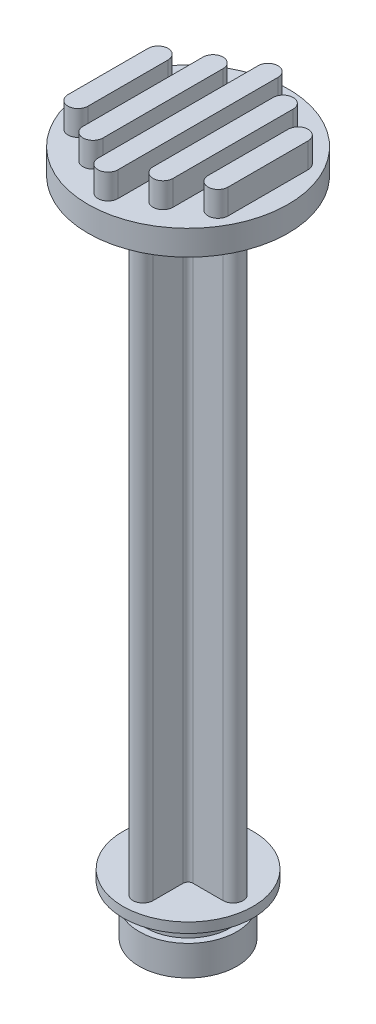
SolidWorks part; units mm, degrees
ref_plane "Front Plane" through (0, 0, 0) normal (0, 0, 1) x (1, 0, 0)
ref_plane "Top Plane" through (0, 0, 0) normal (0, 1, 0) x (1, 0, 0)
ref_plane "Right Plane" through (0, 0, 0) normal (1, 0, 0) x (0, 0, -1)
sketch "Sketch1" plane through (0, 0, 0) normal (0, 0, 1) x (1, 0, 0)
  line L0 (0, 0) -> (4.875, 0)
  line L1 (4.875, 0) -> (4.875, 3)
  line L2 (4.875, 3) -> (4.225, 3)
  line L3 (4.225, 3) -> (4.225, 5)
  line L4 (4.225, 5) -> (6.5, 5)
  line L5 (6.5, 5) -> (6.5, 6)
  line L6 (6.5, 6) -> (0, 6)
  line L7 (0, 6) -> (0, 0)
  dimension "D1" = 6.5
  dimension "D2" = 1
  dimension "D3" = 2
  dimension "D4" = 3
  dimension "D5" = 4.875
  dimension "D6" = 4.225
revolve "Revolve1" add sketch "Sketch1" angle 360 about L7
sketch "Sketch2" plane through (0, 6, 0) normal (0, 1, 0) x (1, 0, 0)
  line L0 (0, 1) -> (0, 0) construction
  line L1 (-1, 0) -> (0, 0) construction
  line L2 (-1, 4.5) -> (-1, 1.5)
  line L3 (-4.5, -1) -> (-1.5, -1)
  line L4 (1, 4.5) -> (1, 1.5)
  line L5 (-4.5, 1) -> (-1.5, 1)
  line L6 (-1, 6.5) -> (-1, -6.5) construction
  line L7 (0, 6.5) -> (0, -6.5) construction
  line L8 (1, 6.5) -> (1, -6.5) construction
  line L9 (-6.5, 1) -> (6.5, 1) construction
  line L10 (-6.5, 0) -> (6.5, 0) construction
  line L11 (-6.5, -1) -> (6.5, -1) construction
  line L12 (1.5, -1) -> (4.5, -1)
  line L13 (0, -1) -> (0, -5.5) construction
  line L14 (1, -1.5) -> (1, -4.5)
  line L15 (1.5, 1) -> (4.5, 1)
  line L16 (-1, -1.5) -> (-1, -4.5)
  arc A1 (1, 4.5) -> (-1, 4.5) centre (0, 4.5) ccw
  arc A2 (4.5, -1) -> (4.5, 1) centre (4.5, 0) ccw
  arc A3 (1, -4.5) -> (-1, -4.5) centre (0, -4.5) cw
  arc A4 (-4.5, -1) -> (-4.5, 1) centre (-4.5, 0) cw
  arc A5 (-1.5, 1) -> (-1, 1.5) centre (-1.5, 1.5) ccw
  arc A6 (1, 1.5) -> (1.5, 1) centre (1.5, 1.5) ccw
  arc A7 (1.5, -1) -> (1, -1.5) centre (1.5, -1.5) ccw
  arc A8 (-1, -1.5) -> (-1.5, -1) centre (-1.5, -1.5) ccw
  point P42 (1, -1)
  point P45 (-1, -1)
  dimension "D5" = 0.5
  dimension "D3" = 4.5
  dimension "D4" = 4.5
  dimension "D1" = 1
  dimension "D2" = 1
extrude "Boss-Extrude1" add sketch "Sketch2" along normal blind 60
sketch "Sketch3" plane through (0, 66, 0) normal (0, 1, 0) x (1, 0, 0)
  circle A0 centre (0, 0) radius 10
  dimension "D1" = 20
extrude "Boss-Extrude2" add sketch "Sketch3" along normal blind 2.5
sketch "Sketch4" plane through (0, 68.5, 0) normal (0, 1, 0) x (1, 0, 0)
  line L0 (0, 6.3392) -> (0, -10) construction
  line L1 (-10, 0) -> (10, 0) construction
  line L2 (-3.5, 4.0448) -> (-3.5, -6.1505) construction
  line L3 (-1, 10) -> (-1, -10) construction
  line L4 (-1, 8) -> (-1, -10)
  line L5 (-4.5, 6) -> (-4.5, -6.1505)
  line L6 (-8, 4) -> (-8, -4)
  line L7 (1, 8) -> (1, -10)
  line L8 (-2.5, 6) -> (-2.5, -6.1505)
  line L9 (-6, -4) -> (-6, 4)
  line L10 (-4.5, 6.5652) -> (-4.5, -6.1505) construction
  line L11 (-3.5, 6.5652) -> (-3.5, -6.1505) construction
  line L12 (-2.5, 6.5652) -> (-2.5, -6.1505) construction
  line L13 (0, 10) -> (0, -10) construction
  line L14 (1, 10) -> (1, -10) construction
  line L15 (7, 0) -> (7, -3.9115) construction
  line L16 (-7, 0) -> (-7, -3.9115) construction
  line L17 (3.5, 4.0448) -> (3.5, -6.1505) construction
  line L18 (6, -4) -> (6, 4)
  line L19 (2.5, 6) -> (2.5, -6.1505)
  line L20 (8, 4) -> (8, -4)
  line L21 (4.5, 6) -> (4.5, -6.1505)
  circle A0 centre (0, 0) radius 10 construction
  arc A1 (1, 8) -> (-1, 8) centre (0, 8) ccw
  arc A2 (-2.5, 6) -> (-4.5, 6) centre (-3.5, 6) ccw
  arc A3 (-6, 4) -> (-8, 4) centre (-7, 4) ccw
  arc A4 (1, -8) -> (-1, -8) centre (0, -8) cw
  arc A5 (-2.5, -6) -> (-4.5, -6) centre (-3.5, -6) cw
  arc A6 (-6, -4) -> (-8, -4) centre (-7, -4) cw
  arc A7 (6, -4) -> (8, -4) centre (7, -4) ccw
  arc A8 (2.5, -6) -> (4.5, -6) centre (3.5, -6) ccw
  arc A9 (6, 4) -> (8, 4) centre (7, 4) cw
  arc A10 (2.5, 6) -> (4.5, 6) centre (3.5, 6) cw
  dimension "D3" = 8
  dimension "D4" = 6
  dimension "D5" = 4
  dimension "D6" = 3.5
  dimension "D7" = 3.5
  dimension "D1" = 1
  dimension "D2" = 1
extrude "Boss-Extrude3" add sketch "Sketch4" along normal blind 2.5 contours A4 L7 A1 L4 | A5 L8 A2 L5 | A10 L19 A8 L21 | A9 L18 A7 L20 | L9 A3 L6 A6
